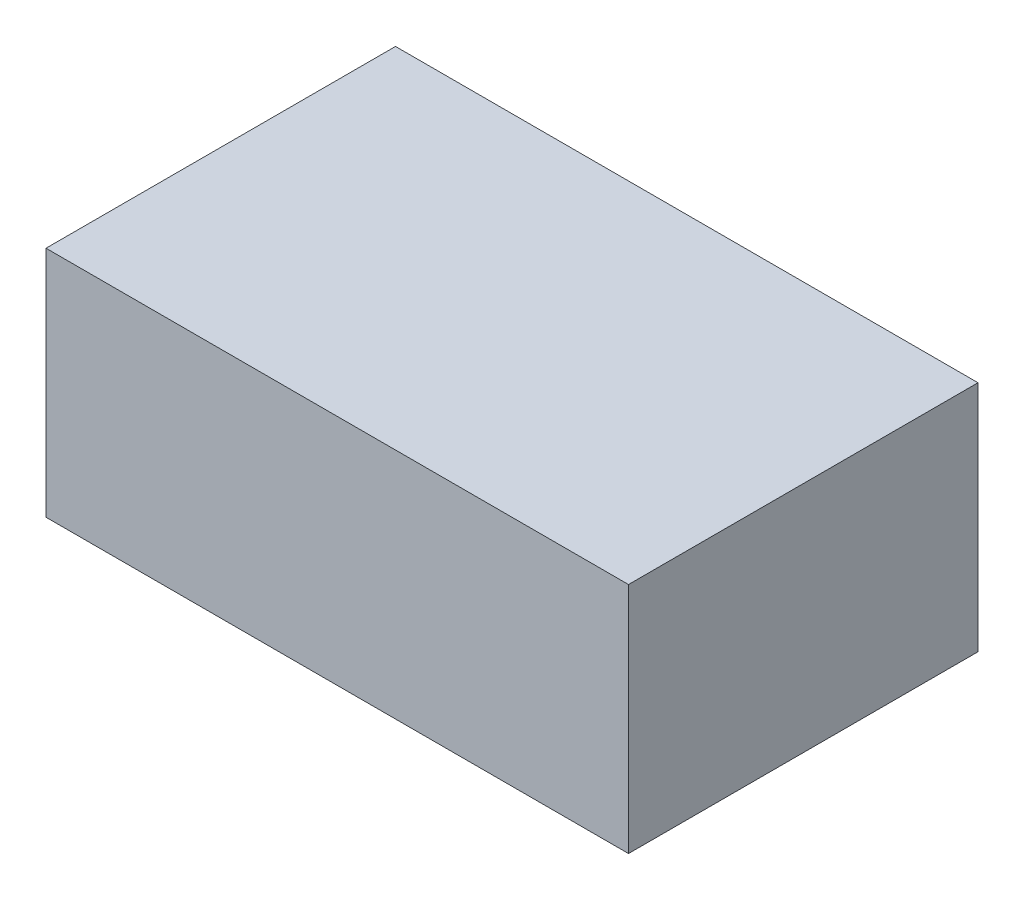
SolidWorks part; units mm, degrees
ref_plane "Front Plane" through (0, 0, 0) normal (0, 0, 1) x (1, 0, 0)
ref_plane "Top Plane" through (0, 0, 0) normal (0, 1, 0) x (1, 0, 0)
ref_plane "Right Plane" through (0, 0, 0) normal (1, 0, 0) x (0, 0, -1)
sketch "Sketch1" plane through (0, 0, 0) normal (0, 1, 0) x (1, 0, 0)
  line L1 (-0.5, 0.3) -> (0.5, 0.3)
  line L2 (-0.5, 0.3) -> (-0.5, -0.3)
  line L3 (-0.5, -0.3) -> (0.5, -0.3)
  line L4 (0.5, 0.3) -> (0.5, -0.3)
  line L5 (-0.5, 0.3) -> (0.5, -0.3) construction
  line L6 (-0.5, -0.3) -> (0.5, 0.3) construction
  point P0 (0, 0)
  dimension "D1" = 1
  dimension "D2" = 0.6
extrude "Boss-Extrude1" add sketch "Sketch1" along normal blind 0.4
sketch "Sketch2" plane through (0, 0, 0) normal (0, -1, 0) x (1, 0, 0)
  line L0 (-0.5, 0) -> (0.5, 0) construction
  line L1 (-0.45, 0.25) -> (-0.2, 0.25)
  line L2 (-0.45, 0.25) -> (-0.45, -0.25)
  line L3 (-0.45, -0.25) -> (-0.2, -0.25)
  line L4 (-0.2, 0.25) -> (-0.2, -0.25)
  line L5 (-0.5, -0.3) -> (-0.5, 0.3) construction
  line L6 (0.5, 0.3) -> (0.5, -0.3) construction
  line L7 (0, 0.3) -> (0, -0.3) construction
  line L8 (-0.5, 0.3) -> (0.5, 0.3) construction
  line L9 (0.5, -0.3) -> (-0.5, -0.3) construction
  line L10 (0.2, 0.25) -> (0.2, -0.25)
  line L11 (0.45, -0.25) -> (0.2, -0.25)
  line L12 (0.45, 0.25) -> (0.45, -0.25)
  line L13 (0.45, 0.25) -> (0.2, 0.25)
  line L14 (-0.325, 0.25) -> (-0.325, -0.25) construction
  line L15 (0.325, 0.25) -> (0.325, -0.25) construction
  point P16 (-0.2, 0)
  dimension "D1" = 0.25
  dimension "D2" = 0.5
  dimension "D3" = 0.65
extrude "Boss-Extrude2" add sketch "Sketch2" along normal blind 0.05
